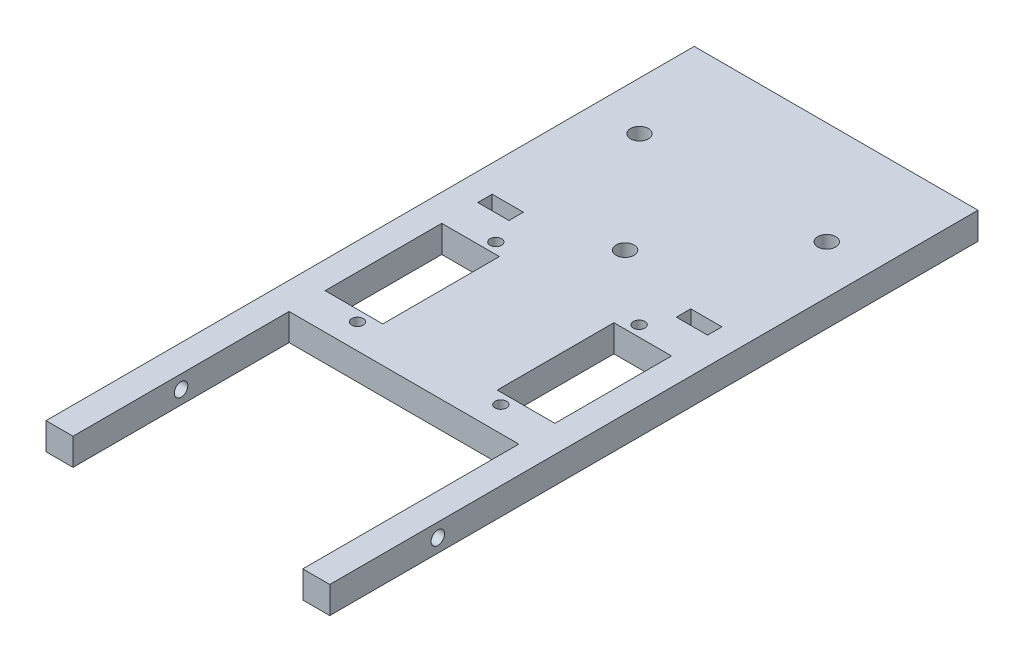
SolidWorks part; units mm, degrees
ref_plane "Front Plane" through (0, 0, 0) normal (0, 0, 1) x (1, 0, 0)
ref_plane "Top Plane" through (0, 0, 0) normal (0, 1, 0) x (1, 0, 0)
ref_plane "Right Plane" through (0, 0, 0) normal (1, 0, 0) x (0, 0, -1)
sketch "Sketch1" plane through (0, 0, 0) normal (0, 1, 0) x (1, 0, 0)
  line L1 (-50.038, 114.3) -> (50.038, 114.3)
  line L2 (-50.038, 114.3) -> (-50.038, -114.3)
  line L3 (-50.038, -114.3) -> (50.038, -114.3)
  line L4 (50.038, 114.3) -> (50.038, -114.3)
  line L5 (-50.038, 114.3) -> (50.038, -114.3) construction
  line L6 (-50.038, -114.3) -> (50.038, 114.3) construction
  point P0 (0, 0)
  dimension "D1" = 100.076
  dimension "D2" = 228.6
extrude "Boss-Extrude1" add sketch "Sketch1" along normal blind 9.525
sketch "Sketch2" plane through (0, 9.525, 0) normal (0, 1, 0) x (1, 0, 0)
  line L0 (-50.038, -114.3) -> (50.038, -114.3) construction
  line L1 (-40.513, -38.1) -> (40.513, -38.1)
  line L2 (-40.513, -38.1) -> (-40.513, -114.3)
  line L3 (-40.513, -114.3) -> (40.513, -114.3)
  line L4 (40.513, -38.1) -> (40.513, -114.3)
  line L5 (-50.038, 114.3) -> (-50.038, -114.3) construction
  line L6 (50.038, -114.3) -> (50.038, 114.3) construction
  dimension "D1" = 9.525
  dimension "D2" = 9.525
  dimension "D3" = 76.2
extrude "Cut-Extrude1" cut sketch "Sketch2" against normal through all
sketch "Sketch3" plane through (0, 9.525, 0) normal (0, 1, 0) x (1, 0, 0)
  line L0 (40.513, -38.1) -> (-40.513, -38.1) construction
  line L1 (-40.513, 15.748) -> (-20.193, 15.748)
  line L2 (-40.513, 15.748) -> (-40.513, -25.4)
  line L3 (-40.513, -25.4) -> (-20.193, -25.4)
  line L4 (-20.193, 15.748) -> (-20.193, -25.4)
  line L5 (-50.038, 114.3) -> (-50.038, -114.3) construction
  line L6 (0, 44.3201) -> (0, -22.352) construction
  line L7 (-40.513, 33.528) -> (-29.5148, 33.528)
  line L8 (-40.513, 33.528) -> (-40.513, 28.448)
  line L9 (-40.513, 28.448) -> (-29.5148, 28.448)
  line L10 (-29.5148, 33.528) -> (-29.5148, 28.448)
  line L11 (20.193, 15.748) -> (20.193, -25.4)
  line L12 (40.513, -25.4) -> (20.193, -25.4)
  line L13 (40.513, 15.748) -> (40.513, -25.4)
  line L14 (40.513, 15.748) -> (20.193, 15.748)
  line L15 (29.5148, 33.528) -> (29.5148, 28.448)
  line L16 (40.513, 28.448) -> (29.5148, 28.448)
  line L17 (40.513, 33.528) -> (40.513, 28.448)
  line L18 (40.513, 33.528) -> (29.5148, 33.528)
  dimension "D1" = 20.32
  dimension "D2" = 41.148
  dimension "D3" = 12.7
  dimension "D4" = 9.525
  dimension "D5" = 10.9982
  dimension "D6" = 5.08
  dimension "D7" = 9.525
  dimension "D8" = 12.7
extrude "Cut-Extrude2" cut sketch "Sketch3" against normal through all
sketch "Sketch4" plane through (-40.513, 0, 0) normal (1, 0, 0) x (0, 0, -1)
  line L0 (-38.1, 0) -> (-38.1, 9.525) construction
  line L1 (-38.1, 9.525) -> (-114.3, 9.525) construction
  circle A0 centre (-76.2, 4.7625) radius 2.3813
  dimension "D1" = 38.1
  dimension "D2" = 4.7625
  dimension "D3" = 4.7625
extrude "Cut-Extrude3" cut sketch "Sketch4" against normal through all both and the other way through all
sketch "Sketch6" plane through (0, 9.525, 0) normal (0, 1, 0) x (1, 0, 0)
  line L0 (-29.5148, 33.528) -> (-40.513, 33.528) construction
  line L3 (0, 0) -> (0, 102.3934) construction
  circle A0 centre (0, 39.878) radius 3.175
  dimension "D2" = 6.35
  dimension "D1" = 6.35
extrude "Cut-Extrude5" cut sketch "Sketch6" against normal through all
sketch "Sketch5" plane through (0, 9.525, 0) normal (0, 1, 0) x (1, 0, 0)
  line L0 (0, 83.2901) -> (0, -71.1487) construction
  line L1 (-20.193, 15.748) -> (-40.513, 15.748) construction
  line L2 (-40.513, -25.4) -> (-20.193, -25.4) construction
  line L3 (-20.193, -25.4) -> (-20.193, 15.748) construction
  circle A2 centre (-25.273, 19.558) radius 2.032
  circle A3 centre (-25.273, -29.21) radius 2.032
  circle A4 centre (25.273, -29.21) radius 2.032
  circle A5 centre (25.273, 19.558) radius 2.032
  circle A6 centre (-33.02, 77.978) radius 3.175
  circle A7 centre (0, 39.878) radius 3.175 construction
  circle A8 centre (33.02, 77.978) radius 3.175
  dimension "D2" = 4.064
  dimension "D3" = 4.064
  dimension "D9" = 6.35
  dimension "D1" = 3.81
  dimension "D4" = 3.81
  dimension "D5" = 5.08
  dimension "D6" = 5.08
  dimension "D7" = 38.1
  dimension "D8" = 33.02
extrude "Cut-Extrude4" cut sketch "Sketch5" against normal through all both and the other way through all
